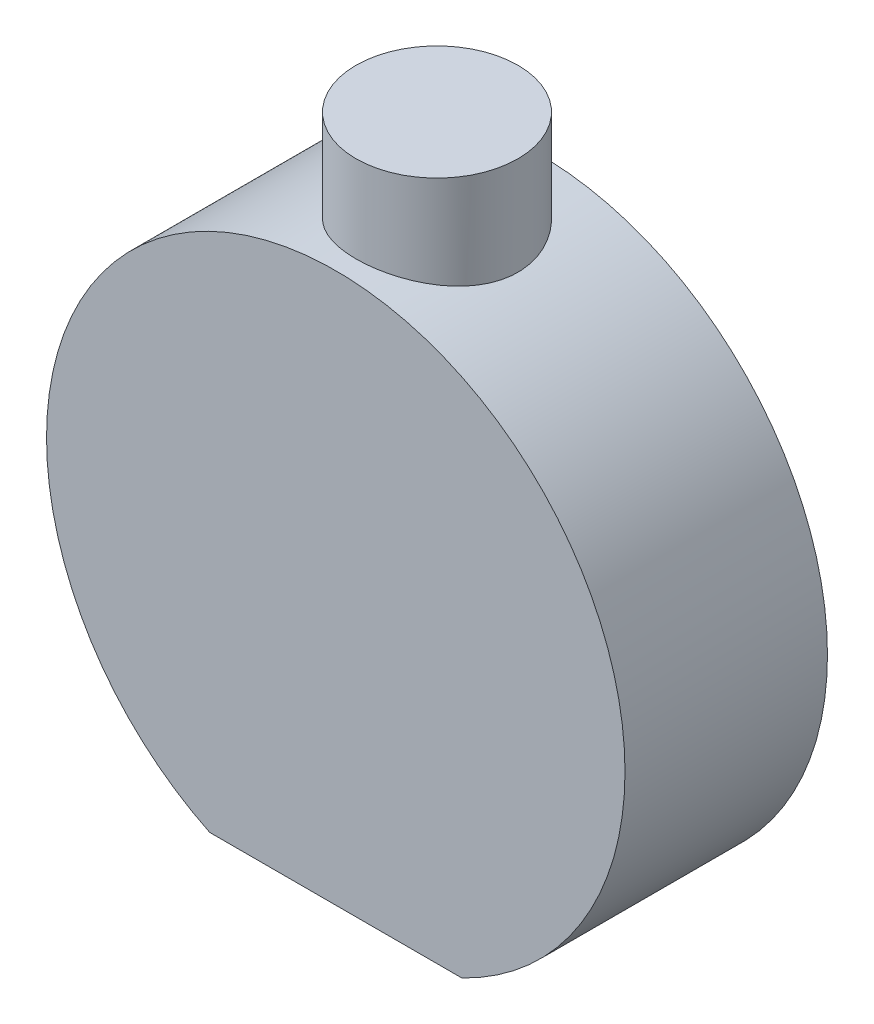
SolidWorks part; units mm, degrees
ref_plane "前视基准面" through (0, 0, 0) normal (0, 0, 1) x (1, 0, 0)
ref_plane "上视基准面" through (0, 0, 0) normal (0, 1, 0) x (1, 0, 0)
ref_plane "右视基准面" through (0, 0, 0) normal (1, 0, 0) x (0, 0, -1)
sketch "草图1" plane through (0, 0, 0) normal (0, 0, 1) x (1, 0, 0)
  circle A0 centre (0, 0) radius 50
  dimension "D1" = 100
extrude "凸台-拉伸1" add sketch "草图1" along normal blind 35
sketch "草图2" plane through (0, 0, 0) normal (0, 1, 0) x (1, 0, 0)
  line L0 (50, 0) -> (-50, 0) construction
  circle A0 centre (0, -17.5) radius 14
  dimension "D1" = 28
  dimension "D2" = 17.5
extrude "凸台-拉伸2" add sketch "草图2" along normal blind 65
sketch "草图3" plane through (0, 65, 0) normal (0, 1, 0) x (1, 0, 0)
  line L1 (-75, 50) -> (75, 50)
  line L2 (-75, 50) -> (-75, -50)
  line L3 (-75, -50) -> (75, -50)
  line L4 (75, 50) -> (75, -50)
  line L5 (-75, 50) -> (75, -50) construction
  line L6 (-75, -50) -> (75, 50) construction
  point P0 (0, 0)
  dimension "D1" = 100
  dimension "D2" = 150
extrude "切除-拉伸1" cut sketch "草图3" against normal blind 64 from offset 110 offset against normal yes
